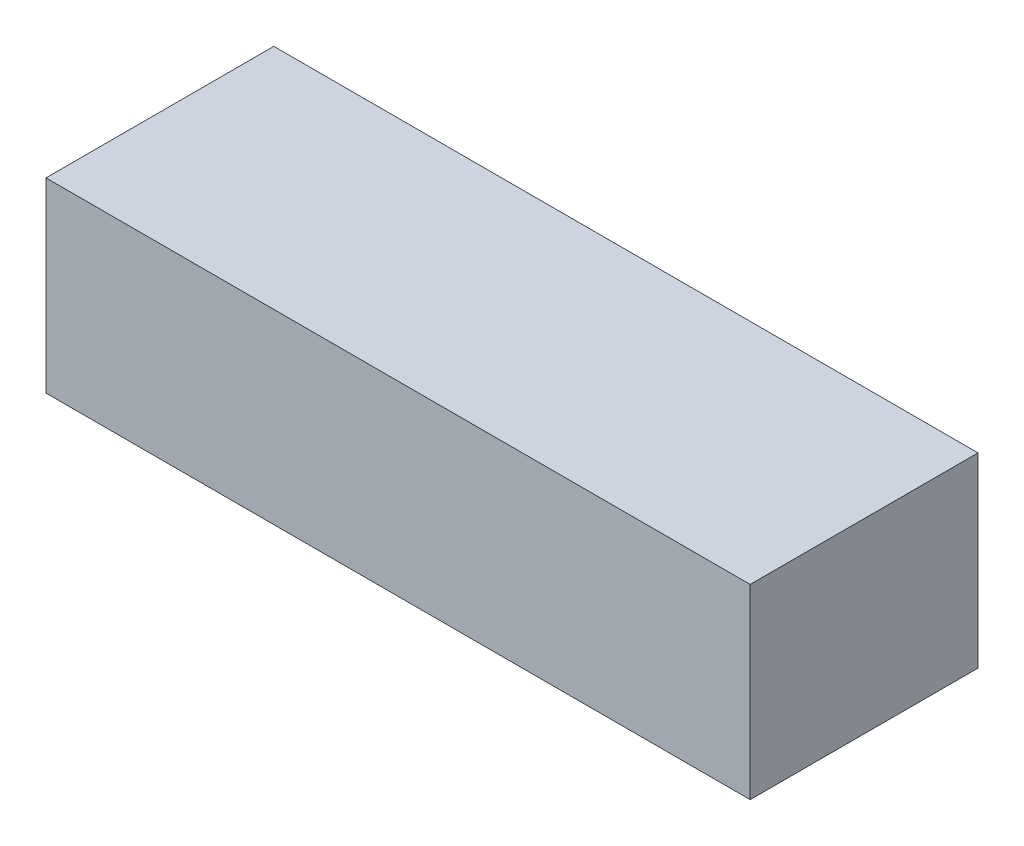
SolidWorks part; units mm, degrees
ref_plane "Front Plane" through (0, 0, 0) normal (0, 0, 1) x (1, 0, 0)
ref_plane "Top Plane" through (0, 0, 0) normal (0, 1, 0) x (1, 0, 0)
ref_plane "Right Plane" through (0, 0, 0) normal (1, 0, 0) x (0, 0, -1)
sketch "Sketch1" plane through (0, 0, 0) normal (0, 1, 0) x (1, 0, 0)
  line L1 (0, 0) -> (102, 0)
  line L2 (0, 0) -> (0, 33)
  line L3 (0, 33) -> (102, 33)
  line L4 (102, 0) -> (102, 33)
extrude "Boss-Extrude1" add sketch "Sketch1" along normal blind 27
